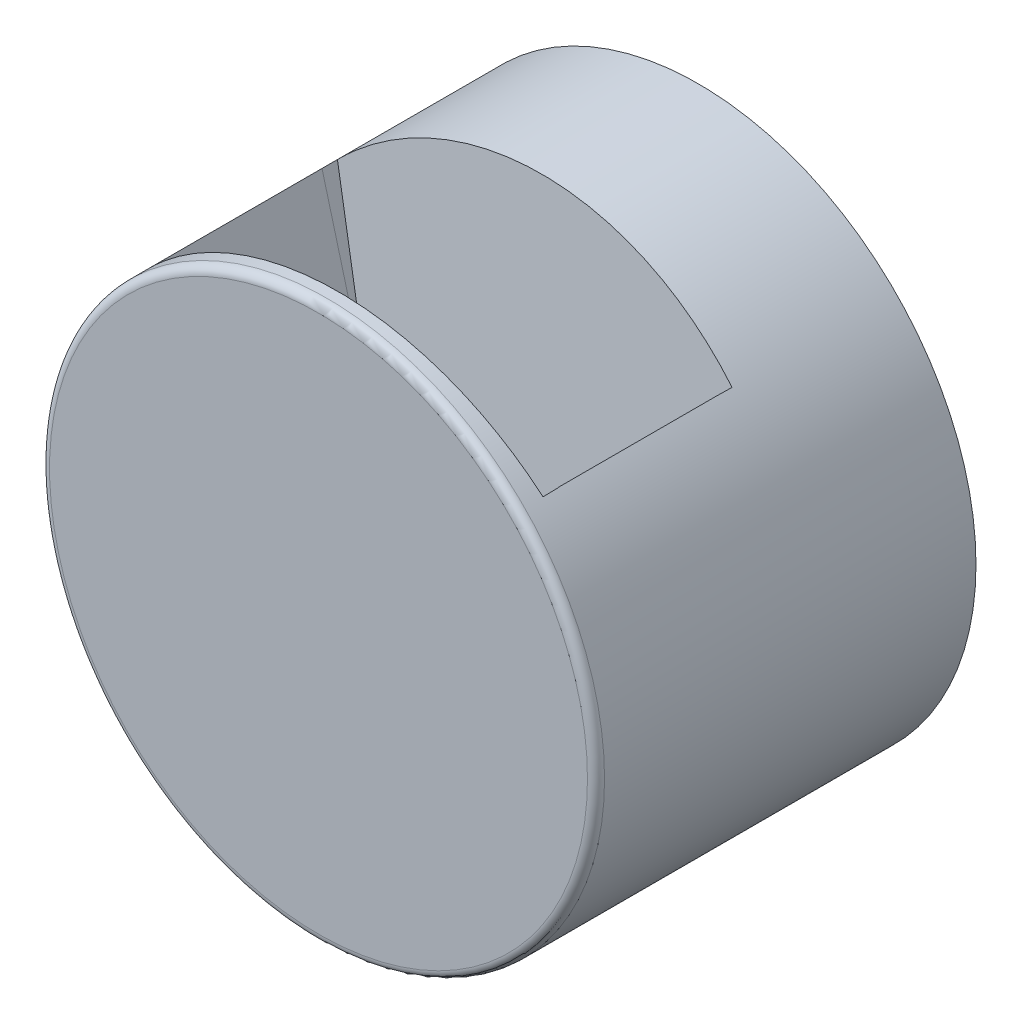
SolidWorks part; units mm, degrees
ref_plane "Front" through (0, 0, 0) normal (0, 0, 1) x (1, 0, 0)
ref_plane "Top" through (0, 0, 0) normal (0, 1, 0) x (1, 0, 0)
ref_plane "Right" through (0, 0, 0) normal (1, 0, 0) x (0, 0, -1)
sketch "草图2" plane through (0, 0, 76.5) normal (0, 0, 1) x (1, 0, 0)
  circle A0 centre (0, 0) radius 32.5
extrude "凸台-拉伸1" add sketch "草图2" along normal blind 3
sketch "草图3" plane through (0, 0, 76.5) normal (0, 0, -1) x (-1, 0, 0)
  circle A0 centre (0, 0) radius 32.5
  circle A1 centre (0, 0) radius 30.5
  dimension "D1" = 61
extrude "凸台-拉伸2" add sketch "草图3" along normal up to surface (43.5 mm away)
sketch "草图4" plane through (0, 0, 0) normal (0, 1, 0) x (1, 0, 0)
  line L10 (17.5, -56) -> (-17.5, -56)
  line L11 (17.5, -56) -> (17.5, -74.5)
  line L12 (17.5, -74.5) -> (-17.5, -74.5)
  line L13 (-17.5, -56) -> (-17.5, -74.5)
  line L14 (17.5, -56) -> (-17.5, -74.5) construction
  line L15 (17.5, -74.5) -> (-17.5, -56) construction
  point P0 (0, -65.25)
extrude "切除-拉伸1" cut sketch "草图4" along normal blind 52
sketch "草图5" plane through (0, 0, 0) normal (0, 1, 0) x (1, 0, 0)
  line L0 (-17.5, -56) -> (-17.5, -74.5) construction
  line L1 (17.5, -56) -> (-17.5, -56)
  line L2 (17.5, -56) -> (17.5, -74.5)
  line L3 (17.5, -74.5) -> (-17.5, -74.5)
  line L4 (-17.5, -56) -> (-17.5, -74.5)
  line L5 (17.5, -56) -> (-17.5, -74.5) construction
  line L6 (17.5, -74.5) -> (-17.5, -56) construction
  line L7 (17.5, -74.5) -> (-17.5, -74.5) construction
  line L8 (30.5, -76.5) -> (-30.5, -76.5) construction
  line L9 (20.5, -54) -> (-20.5, -54)
  line L10 (20.5, -54) -> (20.5, -76.5)
  line L11 (20.5, -76.5) -> (-20.5, -76.5)
  line L12 (-20.5, -54) -> (-20.5, -76.5)
  line L13 (20.5, -54) -> (-20.5, -76.5) construction
  line L14 (20.5, -76.5) -> (-20.5, -54) construction
  line L16 (-17.5, -56) -> (17.5, -56) construction
  line L17 (17.5, -74.5) -> (17.5, -56) construction
  point P0 (0, -65.25)
  point P9 (0, -65.25)
  dimension "D1" = 3
sketch "草图8" plane through (17.5, 0, 0) normal (-1, 0, 0) x (0, 0, 1)
  line L0 (42.2918, 2) -> (84.0986, 2) construction
  line L5 (55.9946, 2) -> (55.9946, 36.438)
  line L6 (55.9946, 36.438) -> (74.5, 36.438)
  line L7 (74.5, 36.438) -> (74.5, 2)
  line L8 (74.5, 27.3861) -> (74.5, 24.98) construction
  line L9 (74.5, 2) -> (55.9946, 2)
extrude "凸台-拉伸3" add sketch "草图5" along normal up to surface (24.98 mm away)
sketch "草图9" plane through (0, 0, 0) normal (0, -1, 0) x (1, 0, 0)
  line L0 (-30.5, 76.5) -> (30.5, 76.5) construction
  line L1 (-21.8071, 53.2753) -> (21.8071, 53.2753)
  line L2 (-21.8071, 53.2753) -> (-21.8071, 76.5)
  line L3 (-21.8071, 76.5) -> (21.8071, 76.5)
  line L4 (21.8071, 53.2753) -> (21.8071, 76.5)
  line L5 (-21.8071, 53.2753) -> (21.8071, 76.5) construction
  line L6 (-21.8071, 76.5) -> (21.8071, 53.2753) construction
  point P0 (0, 64.8877)
extrude "切除-拉伸2" cut sketch "草图9" against normal blind 2
sketch "草图10" plane through (0, 0, 54) normal (0, 0, -1) x (-1, 0, 0)
  line L0 (20.5, 2) -> (30.4344, 2)
  line L1 (-20.5, 2) -> (20.5, 2) construction
  line L2 (20.5, 22.5832) -> (20.5, 2) construction
  line L3 (20.5, 2) -> (20.5, 22.5832)
  line L4 (-20.5, 2) -> (-30.4344, 2)
  line L5 (-20.5, 22.5832) -> (-20.5, 2) construction
  line L6 (-20.5, 2) -> (-20.5, 22.5832)
  arc A0 (30.4344, 2) -> (20.5, 22.5832) centre (0, 0) ccw
  arc A1 (-20.5, 22.5832) -> (-30.4344, 2) centre (0, 0) ccw
extrude "凸台-拉伸4" add sketch "草图10" against normal up to surface (22.5 mm away) up to face at (0, -0.9792, 76.5)
sketch "草图11" plane through (17.5, 0, 0) normal (-1, 0, 0) x (0, 0, 1)
  line L0 (81.9808, 2) -> (50.1533, 2) construction
  line L1 (74.5, 2) -> (56, 2)
  line L2 (74.5, 2) -> (74.5, 38.2916)
  line L3 (74.5, 38.2916) -> (56, 38.2916)
  line L4 (56, 2) -> (56, 38.2916)
revolve "切除-旋转1" cut sketch "草图11" angle 15 about L0
sketch "草图12" plane through (-17.5, 0, 0) normal (1, 0, 0) x (0, 0, -1)
  line L0 (-76.5, 2) -> (-54, 2) construction
  line L1 (-74.5, 2) -> (-56, 2)
  line L2 (-74.5, 2) -> (-74.5, 39.015)
  line L3 (-74.5, 39.015) -> (-56, 39.015)
  line L4 (-56, 2) -> (-56, 39.015)
  line L5 (-74.5, 2) -> (-74.5, 22.8694) construction
  line L6 (-82.2391, 2) -> (-51.0833, 2) construction
revolve "切除-旋转2" cut sketch "草图12" angle 15 about L6
sketch "草图13" plane through (0, 0, 56) normal (0, 0, 1) x (1, 0, 0)
  line L0 (-17.5, 2) -> (17.5, 2)
  line L1 (30.4344, 2) -> (-30.4344, 2) construction
  line L2 (17.5, 2) -> (26.3419, 34.9984)
  line L3 (26.3419, 34.9984) -> (-26.3419, 34.9984)
  line L4 (-17.5, 2) -> (-26.3419, 34.9984)
  line L5 (-38.5808, 2) -> (41.7234, 2) construction
revolve "切除-旋转3" cut sketch "草图13" angle 5 about L5
sketch "草图14" plane through (0, 0, 74.5) normal (0, 0, -1) x (-1, 0, 0)
  line L0 (17.5, 2) -> (-17.5, 2)
  line L1 (-30.4344, 2) -> (30.4344, 2) construction
  line L2 (-17.5, 2) -> (-23.1087, 22.8525) construction
  line L3 (-17.5, 2) -> (-26.5927, 35.8051)
  line L4 (-26.5927, 35.8051) -> (26.5927, 35.8051)
  line L5 (17.5, 2) -> (26.5927, 35.8051)
  line L6 (42.7933, 2) -> (-39.985, 2) construction
revolve "切除-旋转4" cut sketch "草图14" angle 5 about L6
sketch "草图15" plane through (0, 0, 54) normal (0, 0, -1) x (-1, 0, 0)
  line L0 (30.4344, 2) -> (-30.4344, 2)
  line L1 (-30.4344, 2) -> (30.4344, 2) construction
  arc A0 (30.4344, 2) -> (-30.4344, 2) centre (0, 0) ccw
extrude "凸台-拉伸5" add sketch "草图15" along normal blind 3
sketch "草图17" plane through (0, 4.8773, 55.7483) normal (0, 0.0872, 0.9962) x (1, 0, 0)
  line L1 (-18.0871, 33.5647) -> (18.5836, 33.5647)
  line L2 (-18.0871, 33.5647) -> (-18.0871, 8.8812)
  line L3 (-18.0871, 8.8812) -> (18.5836, 8.8812)
  line L4 (18.5836, 33.5647) -> (18.5836, 8.8812)
extrude "切除-拉伸3" cut sketch "草图17" along normal blind 3
chamfer "倒角1" distance 4 angle 45 1 edges at (0, 2, 51)
fillet "圆角1" radius 1 1 edges at (32.5, 0, 79.5)
sketch "草图18" plane through (0, 0, 33) normal (0, 0, -1) x (-1, 0, 0)
  line L0 (0, 38.5589) -> (0, -41.7461) construction
  line L1 (39.51, 0) -> (-41.8156, 0) construction
  circle A1 centre (-29.5, 0) radius 3
  circle A2 centre (0, -29.5) radius 3
  circle A3 centre (0, 0) radius 32.5 construction
  circle A5 centre (29.5, 0) radius 3
  circle A6 centre (0, 29.5) radius 3 [skipped]
  point P17 (0, 0)
  dimension "D1" = 6
  dimension "D2" = 4
extrude "凸台-拉伸6" add sketch "草图18" against normal up to surface (43.5 mm away) up to face at (0, -14.25, 76.5)
sketch "草图19" plane through (0, 0, 33) normal (0, 0, -1) x (-1, 0, 0)
  line L0 (0, 0) -> (0, 32.5) construction
  circle A2 centre (0, 0) radius 32.5 construction
  circle A3 centre (0, 29.5) radius 3
  dimension "D1" = 6
extrude "凸台-拉伸7" add sketch "草图19" against normal up to surface (18 mm away) up to face at (0, 18.25, 51)
sketch "草图20" plane through (0, 0, 33) normal (0, 0, -1) x (-1, 0, 0)
  circle A0 centre (0, -29.5) radius 0.95
  circle A1 centre (29.5, 0) radius 0.95
  circle A2 centre (0, 29.5) radius 0.95
  circle A3 centre (-29.5, 0) radius 0.95
  dimension "D1" = 1.9
  dimension "D2" = 1.9
  dimension "D3" = 1.9
  dimension "D4" = 1.9
extrude "切除-拉伸4" cut sketch "草图20" against normal blind 10
sketch "草图21" plane through (0, 0, 33) normal (0, 0, -1) x (-1, 0, 0)
  circle A0 centre (0, 0) radius 44.198
extrude "切除-拉伸5" cut sketch "草图21" against normal blind 2
